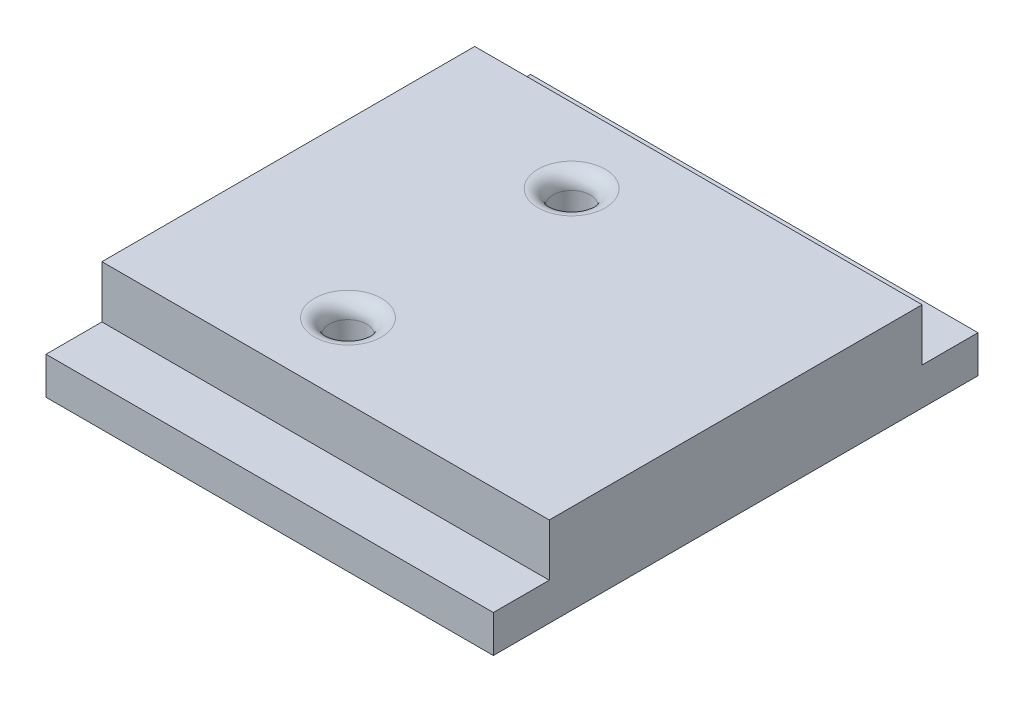
SolidWorks part; units mm, degrees
ref_plane "Front Plane" through (0, 0, 0) normal (0, 0, 1) x (1, 0, 0)
ref_plane "Top Plane" through (0, 0, 0) normal (0, 1, 0) x (1, 0, 0)
ref_plane "Right Plane" through (0, 0, 0) normal (1, 0, 0) x (0, 0, -1)
sketch "Sketch1" plane through (0, 0, 0) normal (1, 0, 0) x (0, 0, -1)
  line L0 (0, 0) -> (-50, 0) construction
  line L1 (-50, 0) -> (0, 0)
  line L2 (0, 0) -> (0, -7)
  line L3 (0, -7) -> (7.5, -7)
  line L4 (-50, 0) -> (-50, -7)
  line L5 (-50, -7) -> (-57.5, -7)
  line L6 (7.5, -7) -> (7.5, -12)
  line L7 (-57.5, -7) -> (-57.5, -12)
  line L8 (-57.5, -12) -> (7.5, -12)
  dimension "D1" = 50
  dimension "D2" = 7
  dimension "D3" = 7.5
  dimension "D4" = 5
extrude "Boss-Extrude1" add sketch "Sketch1" along normal blind 60
sketch "Sketch2" plane through (0, 0, 0) normal (0, 1, 0) x (1, 0, 0)
  line L0 (0, 0) -> (23, 0) construction
  line L1 (60, 0) -> (0, 0) construction
  line L2 (23, -50) -> (23, -40) construction
  line L4 (23, 0) -> (23, -10) construction
  line L5 (60, -50) -> (0, -50) construction
  circle A0 centre (23, -10) radius 2.5
  circle A1 centre (23, -40) radius 2.5
  dimension "D3" = 5
  dimension "D1" = 23
  dimension "D2" = 10
extrude "Cut-Extrude1" cut sketch "Sketch2" against normal through all both and the other way through all
fillet "Fillet1" radius 2 2 edges at (23, 0, 37.5) (23, 0, 7.5)
sketch "Sketch4" plane through (0, -12, 0) normal (0, -1, 0) x (1, 0, 0)
  line L0 (0, 57.5) -> (6.9971, 57.5) construction
  line L1 (60, 57.5) -> (0, 57.5) construction
  line L3 (6.9971, 57.5) -> (60, 57.5)
  line L4 (6.9971, 57.5) -> (6.9971, -7.5)
  line L5 (6.9971, -7.5) -> (60, -7.5)
  line L6 (60, 57.5) -> (60, -7.5)
sketch "Sketch5" plane through (0, 0, 0) normal (0, 1, 0) x (1, 0, 0)
  line L0 (60, -25) -> (0, -25) construction
  line L1 (60, -57.5) -> (60, 7.5) construction
  line L2 (0, 0) -> (0, -50) construction
  line L3 (0, -25) -> (10.0184, -25) construction
